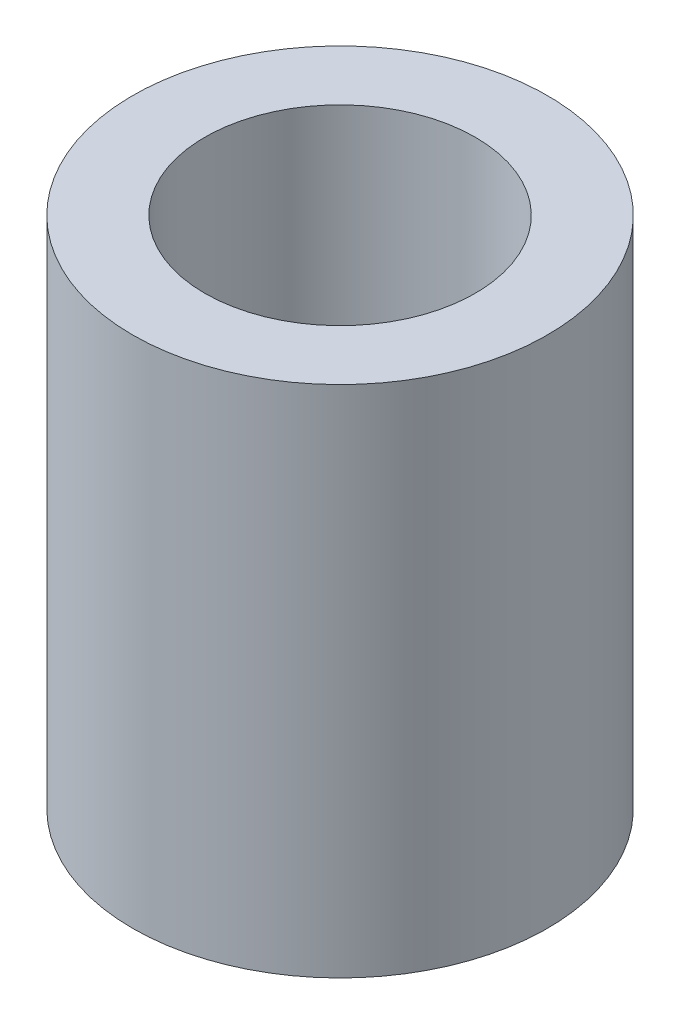
SolidWorks part; units mm, degrees
material "Brass"
ref_plane "Front Plane" through (0, 0, 0) normal (0, 0, 1) x (1, 0, 0)
ref_plane "Top Plane" through (0, 0, 0) normal (0, 1, 0) x (1, 0, 0)
ref_plane "Right Plane" through (0, 0, 0) normal (1, 0, 0) x (0, 0, -1)
sketch "Sketch1" plane through (0, 0, 0) normal (0, 1, 0) x (1, 0, 0)
  circle A0 centre (0, 0) radius 1.5
  circle A1 centre (0, 0) radius 2.3
  dimension "D1" = 4.6
  dimension "D2" = 3
extrude "Boss-Extrude1" add sketch "Sketch1" along normal mid plane 5.7
